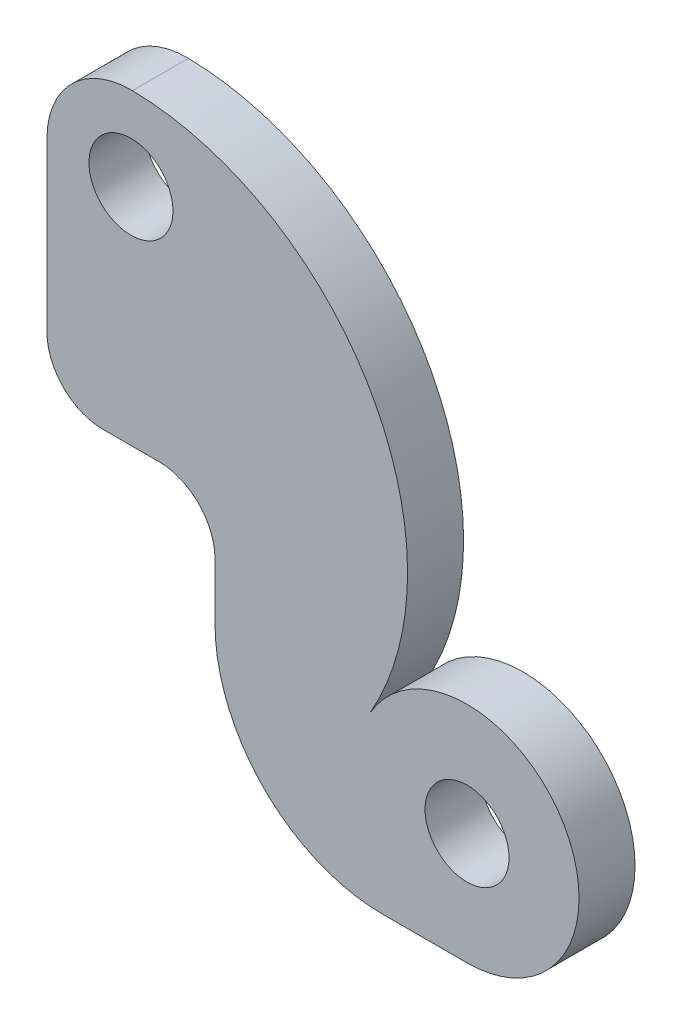
SolidWorks part; units mm, degrees
ref_plane "Front Plane" through (0, 0, 0) normal (0, 0, 1) x (1, 0, 0)
ref_plane "Top Plane" through (0, 0, 0) normal (0, 1, 0) x (1, 0, 0)
ref_plane "Right Plane" through (0, 0, 0) normal (1, 0, 0) x (0, 0, -1)
sketch "Sketch1" plane through (0, 0, 0) normal (0, 0, 1) x (1, 0, 0)
  line L0 (-206.8179, 0) -> (10134.0752, 0) construction
  line L1 (0, -206.8179) -> (0, 10134.0752) construction
  line L2 (-15, 0) -> (-15, -30)
  line L3 (-5, -40) -> (5, -40)
  line L4 (15, -50) -> (15, -60)
  line L5 (45, -90) -> (60, -90)
  circle A0 centre (0, 0) radius 7.5
  arc A1 (0.2651, 14.9977) -> (-15, 0) centre (0, 0) ccw
  circle A2 centre (60, -70) radius 7.5
  arc A3 (60, -90) -> (42.6804, -59.9984) centre (60, -70) ccw
  arc A4 (5, -40) -> (15, -50) centre (5, -50) cw
  arc A5 (-15, -30) -> (-5, -40) centre (-5, -30) ccw
  arc A6 (0.2651, 14.9977) -> (42.6804, -59.9984) centre (-0.6186, -34.9945) cw
  arc A7 (15, -60) -> (45, -90) centre (45, -60) ccw
  point P20 (-15, -40)
  point P26 (15, -90)
  dimension "D1" = 15
  dimension "D2" = 30
  dimension "D3" = 15
  dimension "D4" = 40
  dimension "D10" = 10
  dimension "D11" = 10
  dimension "D12" = 50
  dimension "D13" = 30
  dimension "D5" = 60
  dimension "D6" = 70
  dimension "D7" = 40
  dimension "D8" = 30
  dimension "D9" = 45
extrude "Boss-Extrude1" add sketch "Sketch1" along normal mid plane 10
